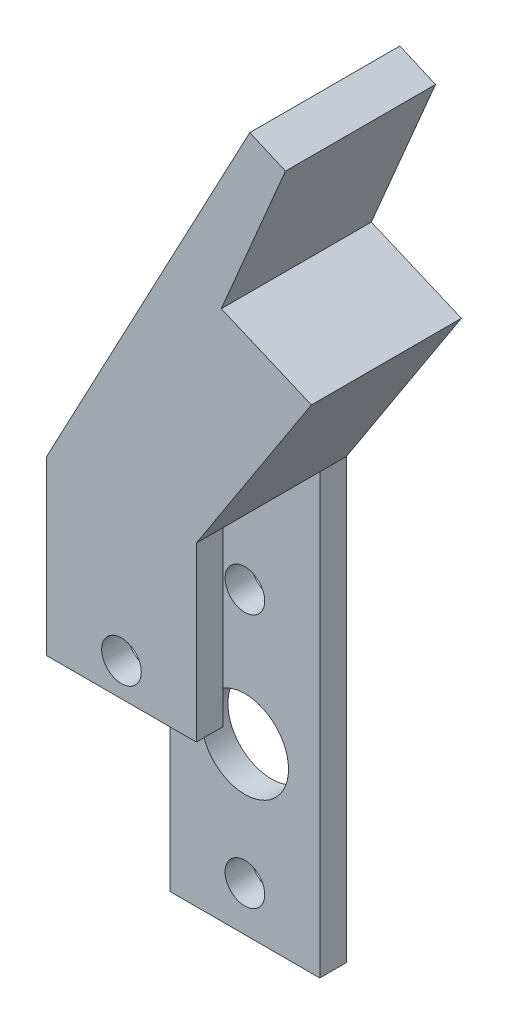
SolidWorks part; units mm, degrees
ref_plane "Front Plane" through (0, 0, 0) normal (0, 0, 1) x (1, 0, 0)
ref_plane "Top Plane" through (0, 0, 0) normal (0, 1, 0) x (1, 0, 0)
ref_plane "Right Plane" through (0, 0, 0) normal (1, 0, 0) x (0, 0, -1)
sketch "Sketch1" plane through (0, 0, 0) normal (0, 0, 1) x (1, 0, 0)
  line L0 (-110.5146, 1.2624) -> (-96.2144, 1.2624)
  line L1 (-96.2144, 1.2624) -> (-96.2144, 43.1216)
  line L2 (-96.2144, 43.1216) -> (-85.2304, 60.0356)
  line L3 (-85.2304, 60.0356) -> (-93.8345, 63.6878)
  line L4 (-93.8345, 63.6878) -> (-87.7011, 78.1372)
  line L5 (-91.1134, 79.6101) -> (-87.7011, 78.1372)
  line L6 (-110.5146, 1.2624) -> (-110.5146, 43.1216)
  line L7 (-110.5146, 43.1216) -> (-91.1134, 79.6101)
extrude "Boss-Extrude1" add sketch "Sketch1" along normal blind 14.3256
sketch "Sketch2" plane through (0, 0, 14.3256) normal (0, 0, 1) x (1, 0, 0)
  line L0 (-103.3645, 1.2624) -> (-103.3645, 5.5296) construction
  line L1 (-110.5146, 1.2624) -> (-96.2144, 1.2624) construction
  line L2 (-103.3645, 5.5296) -> (-103.3645, 17.0358) construction
  line L3 (-103.3645, 17.0358) -> (-103.3645, 29.812) construction
  line L4 (-103.3645, 29.812) -> (-103.3645, 56.569) construction
  line L5 (-91.1134, 79.6101) -> (-110.5146, 43.1216) construction
  circle A0 centre (-103.3645, 5.5296) radius 1.8923
  circle A1 centre (-103.3645, 17.0358) radius 4.1656
  circle A2 centre (-103.3645, 29.812) radius 1.8923
  point P12 (0, 0)
extrude "Cut-Extrude1" cut sketch "Sketch2" against normal blind 14.3256
sketch "Sketch3" plane through (-96.2144, 0, 0) normal (1, 0, 0) x (0, 0, -1)
  line L0 (-14.3256, 1.2624) -> (-11.7856, 1.2624)
  line L1 (-14.3256, 1.2624) -> (0, 1.2624) construction
  line L2 (-11.7856, 1.2624) -> (-2.54, 1.2624)
  line L3 (-2.54, 1.2624) -> (0, 1.2624)
  line L4 (-11.7856, 1.2624) -> (-11.7856, 43.1216)
  line L5 (-11.7856, 43.1216) -> (-2.54, 43.1216)
  line L6 (-2.54, 43.1216) -> (-2.54, 1.2624)
  line M2 (0, 43.1216) -> (-14.3256, 43.1216)
  line M4 (-14.3256, 1.2624) -> (0, 1.2624)
extrude "Cut-Extrude2" cut sketch "Sketch3" against normal blind 14.3256 contours L6 L4 M2 M4
sketch "Sketch4" plane through (-96.2144, 0, 0) normal (1, 0, 0) x (0, 0, -1)
  line L0 (-14.3256, 1.2624) -> (-14.3256, 26.6624)
  line L1 (-14.3256, 1.2624) -> (-14.3256, 43.1216) construction
  line L2 (-14.3256, 26.6624) -> (-11.7856, 26.6624)
  line L3 (-11.7856, 1.2624) -> (-11.7856, 43.1216) construction
  line L4 (-11.7856, 26.6624) -> (-11.7856, 1.2624)
  line L5 (-11.7856, 26.6624) -> (-11.7856, 1.2624)
  line L6 (-14.3256, 1.2624) -> (-14.3256, 26.6624)
  line M1 (-11.7856, 1.2624) -> (-11.7856, 43.1216)
  line M3 (-14.3256, 43.1216) -> (-14.3256, 1.2624)
  line M4 (-14.3256, 1.2624) -> (-11.7856, 1.2624)
extrude "Cut-Extrude3" cut sketch "Sketch4" against normal blind 14.3256 contours L2 M3 M4 M1
